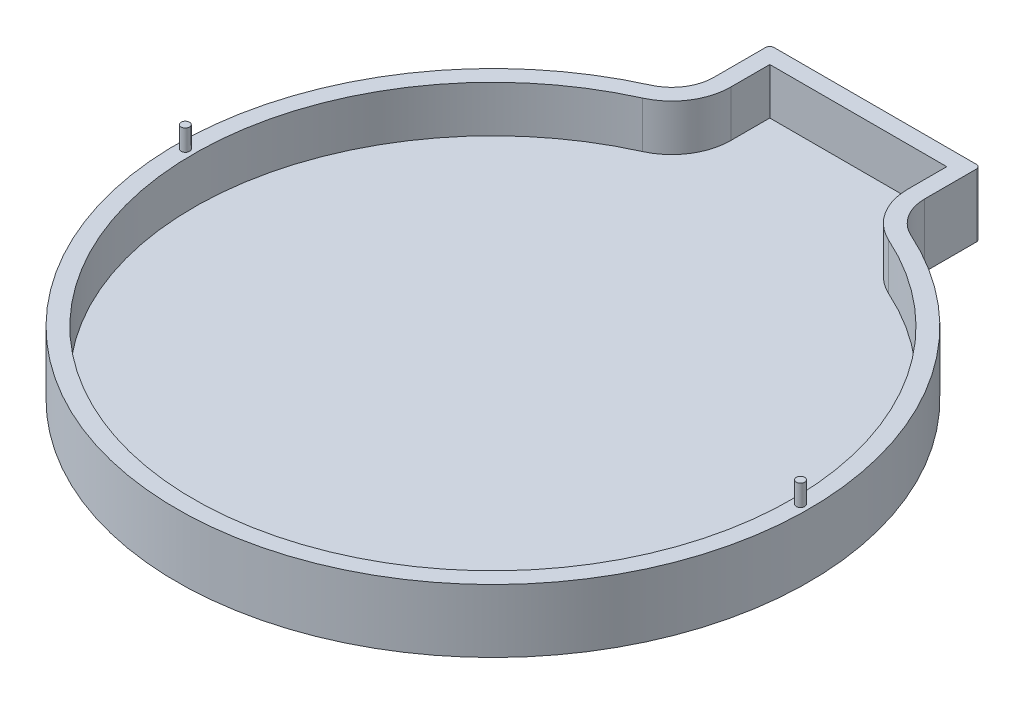
SolidWorks part; units mm, degrees
ref_plane "Front" through (0, 0, 0) normal (0, 0, 1) x (1, 0, 0)
ref_plane "Top" through (0, 0, 0) normal (0, 1, 0) x (1, 0, 0)
ref_plane "Right" through (0, 0, 0) normal (1, 0, 0) x (0, 0, -1)
sketch "Sketch1" plane through (0, 0, 0) normal (0, 1, 0) x (1, 0, 0)
  line L1 (-24, 90.7107) -> (24, 90.7107)
  line L2 (-25, 89.7107) -> (-25, 70.7107)
  line L4 (25, 89.7107) -> (25, 70.7107)
  arc A0 (-25, 70.7107) -> (25, 70.7107) centre (0, 0) ccw
  arc A2 (24, 90.7107) -> (25, 89.7107) centre (24, 89.7107) cw
  arc A3 (-24, 90.7107) -> (-25, 89.7107) centre (-24, 89.7107) ccw
  point P5 (0, 90.7107)
  point P12 (25, 90.7107)
  point P15 (-25, 90.7107)
  dimension "D1" = 150
  dimension "D5" = 1
  dimension "D3" = 50
  dimension "D4" = 20
extrude "Boss-Extrude1" add sketch "Sketch1" along normal blind 15
fillet "Fillet2" radius 10 2 edges at (25, 7.5, -70.7107) (-25, 7.5, -70.7107)
shell "Shell1" thickness 4
sketch "Sketch7" plane through (0, 15, 0) normal (0, 1, 0) x (1, 0, 0)
  line L0 (-75, 0) -> (75, 0) construction
  arc A0 (-30.8824, 68.3468) -> (30.8824, 68.3468) centre (0, 0) ccw construction
  circle A1 centre (-73, 0) radius 1
  circle A2 centre (73, 0) radius 1
  dimension "D1" = 2
  dimension "D2" = 2
  dimension "D3" = 2
  dimension "D4" = 2
extrude "Boss-Extrude4" add sketch "Sketch7" along normal blind 5
